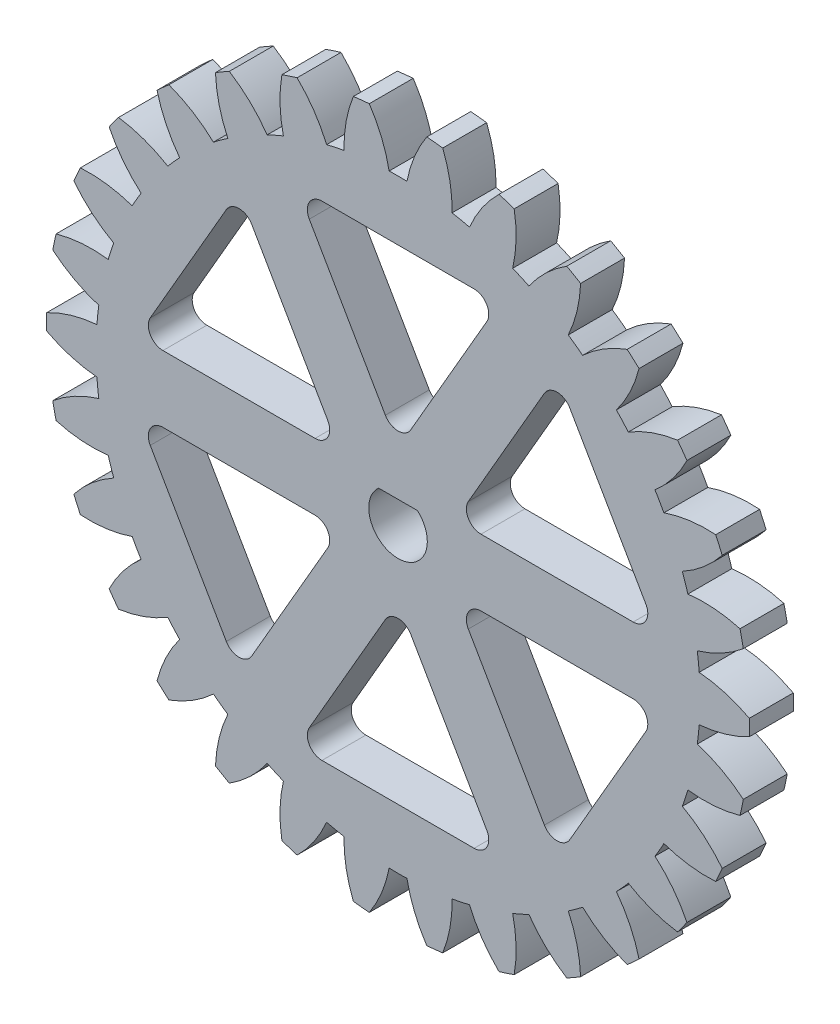
SolidWorks part; units mm, degrees
ref_plane "Front Plane" through (0, 0, 0) normal (0, 0, 1) x (1, 0, 0)
ref_plane "Top Plane" through (0, 0, 0) normal (0, 1, 0) x (1, 0, 0)
ref_plane "Right Plane" through (0, 0, 0) normal (1, 0, 0) x (0, 0, -1)
sketch "Sketch1" plane through (0, 0, 0) normal (0, 0, 1) x (1, 0, 0)
  circle A0 centre (0, 0) radius 24
  dimension "D1" = 48
extrude "Boss-Extrude1" add sketch "Sketch1" along normal blind 3 contours A0
sketch "Sketch7" plane through (0, 0, 3) normal (0, 0, 1) x (1, 0, 0)
  line L0 (0, 0) -> (0, 29.6766) construction
  line L1 (0, 0) -> (-2.0902, 19.8869) construction
  line L2 (-2.3487, 22.346) -> (-1.177, 22.4692) construction
  circle A0 centre (0, 0) radius 20.625 construction
  circle A1 centre (0, 0) radius 21.1431 construction
  circle A2 centre (0, 0) radius 22.5 construction
  arc A3 (-1.965, 23.9194) -> (-0.6079, 20.616) centre (-9.4458, 18.9158) cw
  circle A4 centre (0, 0) radius 24 construction
  arc A5 (1.965, 23.9194) -> (0.6079, 20.616) centre (9.4458, 18.9158) ccw
  arc A6 (1.965, 23.9194) -> (-1.965, 23.9194) centre (0, 0) ccw
  arc A7 (-0.6079, 20.616) -> (0.6079, 20.616) centre (0, 0) cw
  dimension "D1" = 41.25
  dimension "D2" = 42.2862
  dimension "D3" = 45
  dimension "D4" = 9
  dimension "D6" = 1.1781
  dimension "D5" = 6
extrude "Cut-Extrude1" cut sketch "Sketch7" against normal through all contours A6 A3 A7 A5
pattern_circular "CirPattern1" count 30 over 360 about axis through (0, 0, 0) along (0, 0, 1) of "Cut-Extrude1"
sketch "Sketch8" plane through (0, 0, 3) normal (0, 0, 1) x (1, 0, 0)
  line L0 (0, 4.5428) -> (-6.9282, 16.5428)
  line L1 (-6.9282, 16.5428) -> (6.9282, 16.5428)
  line L2 (6.9282, 16.5428) -> (0, 4.5428)
  line L3 (0, 24.9369) -> (0, -26.0232) construction
  dimension "D1" = 12
extrude "Cut-Extrude3" cut sketch "Sketch8" against normal through all contours L1 L2 L0
fillet "Fillet1" radius 1 3 edges at (6.9282, 16.5428, 1.5) (-6.9282, 16.5428, 1.5) (0, 4.5428, 1.5)
pattern_circular "CirPattern4" count 6 over 360 about axis through (0, 0, 0) along (0, 0, 1) of "Cut-Extrude3", "Fillet1"
sketch "Sketch9" plane through (0, 0, 0) normal (0, 0, -1) x (-1, 0, 0)
  line L0 (-1.3229, 1.5) -> (1.3229, 1.5)
  arc A0 (-1.3229, 1.5) -> (1.3229, 1.5) centre (0, 0) ccw
  dimension "D1" = 4
  dimension "D2" = 1.5
extrude "Cut-Extrude4" cut sketch "Sketch9" against normal blind 10
sketch "Sketch10" [suppressed] plane through (0, 0, 0) normal (0, 0, -1) x (-1, 0, 0)
  line L0 (-1.3229, 1.5) -> (1.3229, 1.5)
  arc A0 (-1.3229, 1.5) -> (1.3229, 1.5) centre (0, 0) ccw
  dimension "D1" = 4
  dimension "D2" = 1.5
extrude "Cut-Extrude5" [suppressed] cut sketch "Sketch10" against normal blind 10 contours L0 A0
sketch "Sketch11" [suppressed] plane through (0, 0, 0) normal (0, 0, -1) x (-1, 0, 0)
  line L0 (-1.3229, 1.5) -> (1.3229, 1.5)
  arc A0 (-1.3229, 1.5) -> (1.3229, 1.5) centre (0, 0) ccw
  dimension "D1" = 4
  dimension "D2" = 1.5
extrude "Cut-Extrude6" [suppressed] cut sketch "Sketch11" against normal blind 10
sketch "Sketch12" [suppressed] plane through (0, 0, 0) normal (0, 0, -1) x (-1, 0, 0)
  line L0 (-1.3379, 1.5) -> (1.3078, 1.5)
  arc A0 (-1.3379, 1.5) -> (1.3078, 1.5) centre (-0.0151, 0) ccw
  dimension "D1" = 4
  dimension "D2" = 1.5
  dimension "D3" = 0
extrude "Cut-Extrude7" [suppressed] cut sketch "Sketch12" against normal blind 10
equation "\"module\" = 1.5"
equation "\"teeth\"= 30"
equation "\"pressureAngle\"= 20deg"
equation "\"gearThickness\"=3"
equation "\"addendumFactor\"= 1"
equation "\"dedendumFactor\"= 1.25"
equation "\"pitch\"= 1 / \"module\""
equation "\"pitchDiameter\"= \"teeth\" / \"pitch\""
equation "\"addendum\"= \"addendumFactor\" / \"pitch\""
equation "\"dedendum\"= \"dedendumFactor\" / \"pitch\""
equation "\"D1@Boss-Extrude1\"=\"gearThickness\""
equation "\"D1@Sketch1\"=\"pitchDiameter\" + 2 * \"addendum\""
equation "\"D1@Sketch7\"=\"pitchDiameter\" - 2 * \"dedendum\""
equation "\"D2@Sketch7\"=\"pitchDiameter\" * cos ( \"pressureAngle\" )"
equation "\"D3@Sketch7\"=\"pitchDiameter\""
equation "\"D4@Sketch7\"=\"pitchDiameter\"/5"
equation "\"D6@Sketch7\"=PI/2/\"pitch\"/2"
equation "\"D5@Sketch7\"=180/\"teeth\""
equation "\"D1@CirPattern1\"= \"teeth\""
